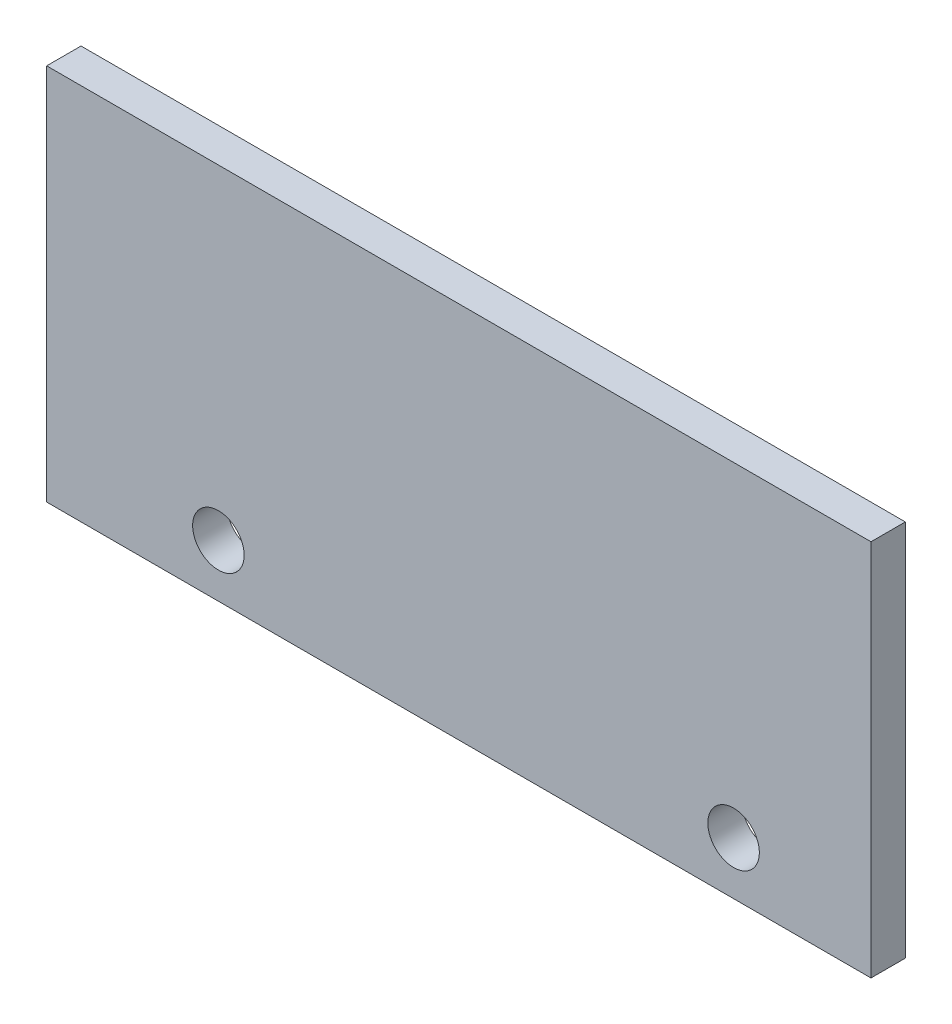
SolidWorks part; units mm, degrees
ref_plane "Front Plane" through (0, 0, 0) normal (0, 0, 1) x (1, 0, 0)
ref_plane "Top Plane" through (0, 0, 0) normal (0, 1, 0) x (1, 0, 0)
ref_plane "Right Plane" through (0, 0, 0) normal (1, 0, 0) x (0, 0, -1)
sketch "Sketch1" plane through (0, 0, 0) normal (0, 0, 1) x (1, 0, 0)
  line L0 (1117.6, 330.2) -> (-50.8, 330.2) construction
  line L1 (673.1, 330.2) -> (825.5, 330.2)
  line L2 (673.1, 330.2) -> (673.1, 260.35)
  line L3 (673.1, 260.35) -> (825.5, 260.35)
  line L4 (825.5, 330.2) -> (825.5, 260.35)
  line L5 (-50.8, 330.2) -> (-50.8, 279.4) construction
  dimension "D1" = 69.85
  dimension "D2" = 152.4
  dimension "D3" = 723.9
extrude "Extrude1" add sketch "Sketch1" along normal blind 6.35
sketch "Sketch2" plane through (0, 0, 6.35) normal (0, 0, 1) x (1, 0, 0)
  circle A0 centre (800.1, 270.0973) radius 4.7625
  circle A1 centre (704.85, 270.0973) radius 4.7625
  dimension "D1" = 9.525
extrude "Cut-Extrude1" cut sketch "Sketch2" against normal through all
